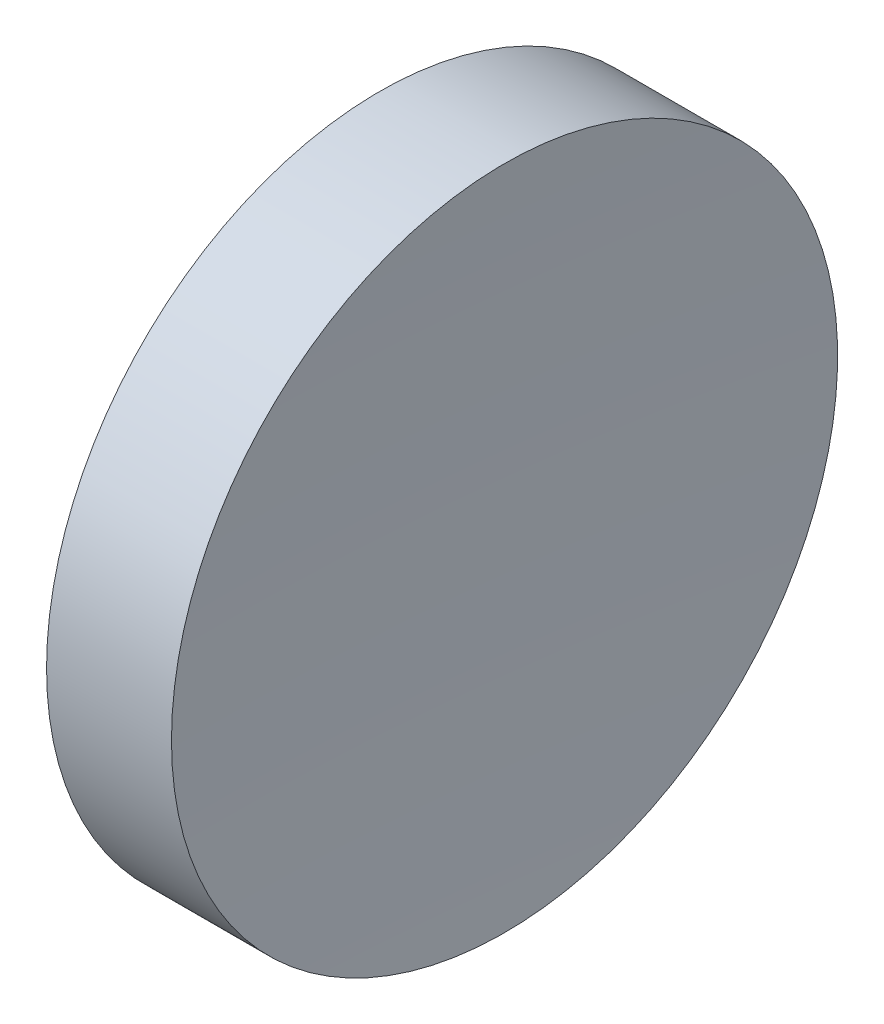
SolidWorks part; units mm, degrees
ref_plane "前视基准面" through (0, 0, 0) normal (0, 0, 1) x (1, 0, 0)
ref_plane "上视基准面" through (0, 0, 0) normal (0, 1, 0) x (1, 0, 0)
ref_plane "右视基准面" through (0, 0, 0) normal (1, 0, 0) x (0, 0, -1)
sketch "草图1" plane through (0, 0, 0) normal (0, 1, 0) x (1, 0, 0)
  line L0 (0, 0) -> (6.9328, 0) construction
  line L1 (0, 0) -> (8.88, 0)
  line L2 (0, 0) -> (0, 25.4)
  line L3 (0, 25.4) -> (9.5256, 25.4)
  arc A0 (9.5256, 25.4) -> (8.88, 0) centre (508.88, 0) ccw
  dimension "D3" = 500
  dimension "D1" = 8.88
  dimension "D2" = 25.4
revolve "旋转1" add sketch "草图1" angle 360 about L0
